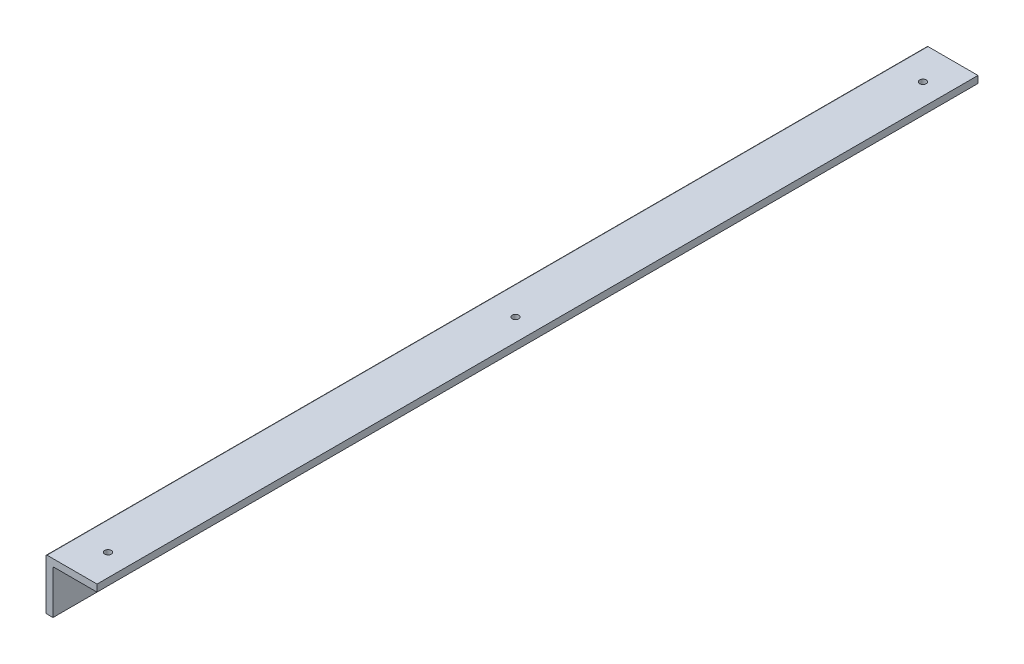
SolidWorks part; units mm, degrees
ref_plane "Front Plane" through (0, 0, 0) normal (0, 0, 1) x (1, 0, 0)
ref_plane "Top Plane" through (0, 0, 0) normal (0, 1, 0) x (1, 0, 0)
ref_plane "Right Plane" through (0, 0, 0) normal (1, 0, 0) x (0, 0, -1)
sketch "Sketch1" plane through (0, 0, 0) normal (0, 0, 1) x (1, 0, 0)
  line L1 (0, 0) -> (3.175, 0)
  line L2 (0, 0) -> (0, 20)
  line L3 (0, 20) -> (3.175, 20)
  line L4 (3.175, 0) -> (3.175, 20)
  line L5 (0, 20) -> (23.175, 20)
  line L6 (0, 20) -> (0, 23.175)
  line L7 (0, 23.175) -> (23.175, 23.175)
  line L8 (23.175, 20) -> (23.175, 23.175)
  dimension "D1" = 20
  dimension "D2" = 3.175
  dimension "D3" = 3.175
  dimension "D4" = 23.175
extrude "Boss-Extrude1" add sketch "Sketch1" along normal blind 400 contours L1 L4 L3 L2 | L5 L8 L7 L6 L3
sketch "Sketch3" plane through (0, 23.175, 0) normal (0, 1, 0) x (1, 0, 0)
  line L1 (23.175, -400) -> (23.175, 0) construction
  circle A0 centre (13.175, -200) radius 1.5
  circle A1 centre (13.175, -385) radius 1.5
  circle A2 centre (13.175, -15) radius 1.5
  dimension "D1" = 3
  dimension "D3" = 3
  dimension "D5" = 3
  dimension "D2" = 10
  dimension "D4" = 185
  dimension "D6" = 185
extrude "Cut-Extrude1" cut sketch "Sketch3" against normal blind 400
sketch "Sketch4" plane through (3.175, 0, 0) normal (1, 0, 0) x (0, 0, -1)
  circle A0 centre (-385, 10) radius 1.5
  circle A1 centre (-200, 10) radius 1.5
  circle A2 centre (-15, 10) radius 1.5
  point P6 (0, 0)
  dimension "D1" = 3
  dimension "D2" = 3
  dimension "D3" = 3
  dimension "D4" = 185
  dimension "D5" = 185
extrude "Cut-Extrude2" cut sketch "Sketch4" against normal blind 400
fillet "Fillet1" radius 0.5 2 edges at (3.175, 20, 200) (0, 23.175, 200)
